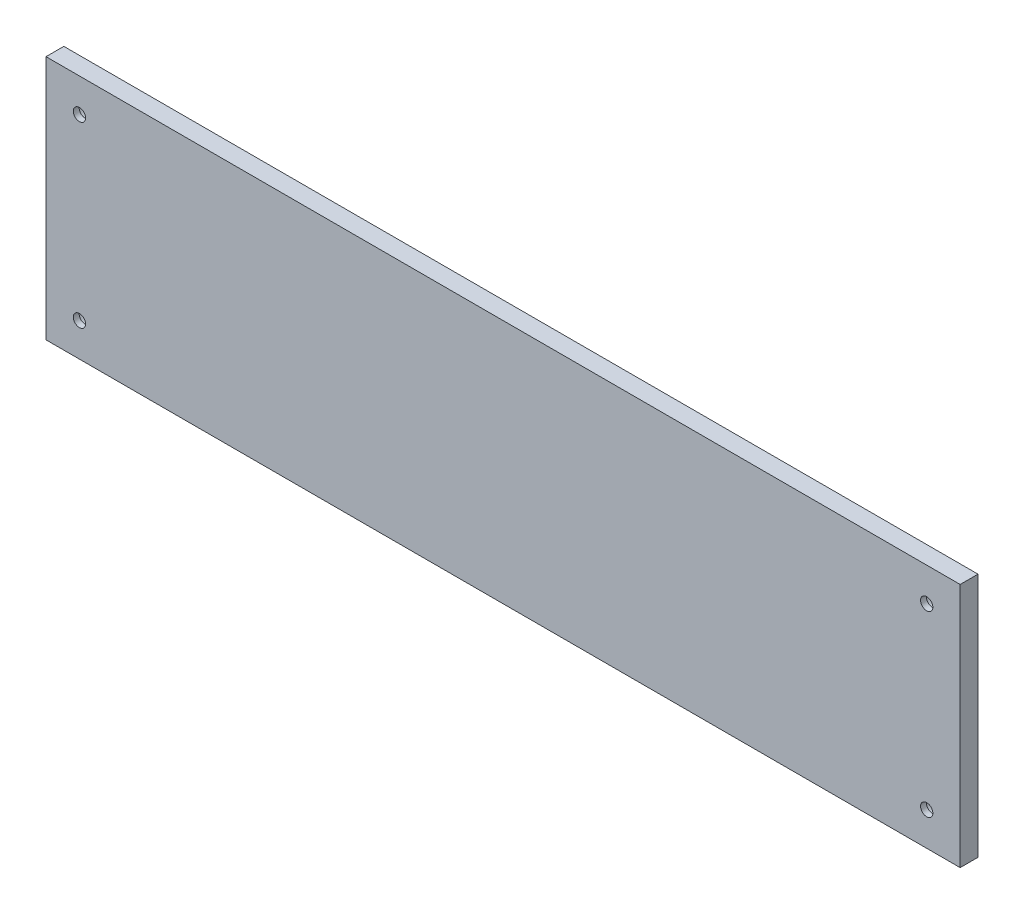
SolidWorks part; units mm, degrees
ref_plane "Front Plane" through (0, 0, 0) normal (0, 0, 1) x (1, 0, 0)
ref_plane "Top Plane" through (0, 0, 0) normal (0, 1, 0) x (1, 0, 0)
ref_plane "Right Plane" through (0, 0, 0) normal (1, 0, 0) x (0, 0, -1)
sketch "Sketch1" plane through (0, 0, 0) normal (0, 0, 1) x (1, 0, 0)
  line L1 (0, 0) -> (410, 0)
  line L2 (0, 0) -> (0, 110)
  line L3 (0, 110) -> (410, 110)
  line L4 (410, 0) -> (410, 110)
extrude "Extrude2" add sketch "Sketch1" along normal blind 8
sketch "Sketch3" plane through (0, 0, 0) normal (0, 0, -1) x (-1, 0, 0)
  line L0 (-395, 95) -> (-15, 95) construction
  line L1 (-15, 95) -> (-15, 15) construction
  line L2 (-15, 15) -> (-395, 15) construction
  line L3 (-395, 15) -> (-395, 95) construction
hole_wizard "CBORE for M5 Hex Socket Head Cap Screw1" positions "3DSketch1" profile "Sketch4" counterbore size "M5" standard "DIN" end condition through all
sketch3d "3DSketch1"
  point P0 (395, 95, 0)
  point P3 (15, 95, 0)
  point P6 (15, 15, 0)
  point P9 (395, 15, 0)
sketch "Sketch4" plane through (395, 95, 0) normal (1, 0, 0) x (0, 1, 0)
  line L0 (0, 0) -> (0, 8)
  line L1 (0, 8) -> (2.75, 8)
  line L3 (2.75, 8) -> (2.75, 5.4)
  line L4 (2.75, 5.4) -> (5, 5.4)
  line L5 (5, 5.4) -> (5, 0)
  line L7 (5, 0) -> (0, 0)
  line L11 (0, -6.35) -> (0, 107.95) construction
  dimension "Thru Hole Dia." = 5.5
  dimension "Thru Hole Depth" = 8
  dimension "C'Bore Dia." = 10
  dimension "C'Bore Depth" = 5.4
